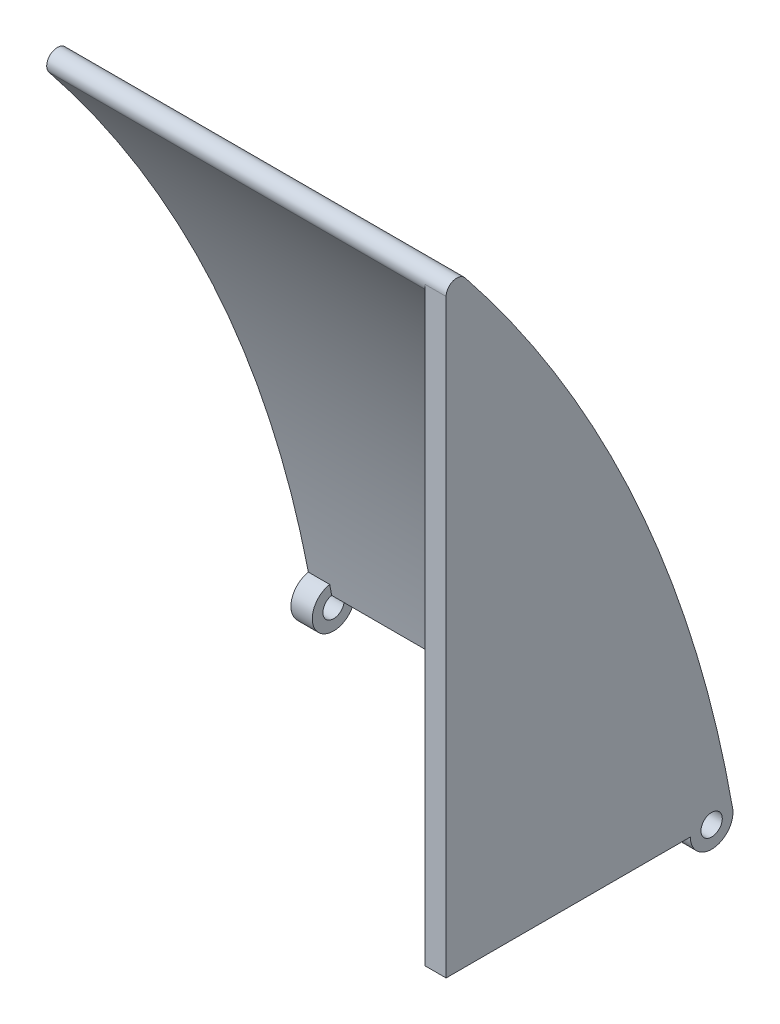
SolidWorks part; units mm, degrees
ref_plane "Front Plane" through (0, 0, 0) normal (0, 0, 1) x (1, 0, 0)
ref_plane "Top Plane" through (0, 0, 0) normal (0, 1, 0) x (1, 0, 0)
ref_plane "Right Plane" through (0, 0, 0) normal (1, 0, 0) x (0, 0, -1)
sketch "Sketch9" plane through (0, 0, 0) normal (1, 0, 0) x (0, 0, -1)
  line L0 (0, 0) -> (-50000, 0) construction
  line L1 (0, 0) -> (0, 50000) construction
  line L2 (0, 0) -> (-0.1736, 0.9848)
  line L3 (-5.0771, 0) -> (-5.0977, 0.1166)
  line L4 (0, 0) -> (-5.0771, 0)
  line L7 (-4.924, -0.8682) -> (-5.0977, 0.1166) construction
  arc A0 (-0.1736, 0.9848) -> (-62.9066, 140) centre (-304.4663, -52.6702) ccw
  arc A1 (-5.0977, 0.1166) -> (-66.8155, 136.8822) centre (-304.4663, -52.6702) ccw
  arc A2 (-66.8155, 136.8822) -> (-62.9066, 140) centre (-64.8611, 138.4411) cw
  dimension "D1" = 10
  dimension "D2" = 1
  dimension "D3" = 140
  dimension "D5" = 66.8155
  dimension "D4" = 5
extrude "Boss-Extrude8" add sketch "Sketch9" along normal mid plane 93.68
sketch "Sketch10" plane through (46.84, 0, 0) normal (1, 0, 0) x (0, 0, -1)
  circle A0 centre (-5.0771, 0) radius 5
  dimension "D1" = 10
extrude "Boss-Extrude9" add sketch "Sketch10" against normal blind 5
mirror "Mirror1" about plane through (0, 0, 0) normal (1, 0, 0) of "Boss-Extrude9"
sketch "Sketch11" plane through (46.84, 0, 0) normal (1, 0, 0) x (0, 0, -1)
  circle A1 centre (-5.0771, 0) radius 2.5
  dimension "D1" = 5
extrude "Cut-Extrude4" cut sketch "Sketch11" against normal through all
sketch "Sketch13" plane through (46.84, 0, 0) normal (1, 0, 0) x (0, 0, -1)
  line L0 (-10.0771, 0) -> (-67.3611, 0)
  line L1 (-67.3611, 0) -> (-67.3611, 138.4411)
  line L2 (-64.8611, 138.4411) -> (-67.3611, 138.4411) construction
  line L3 (-5.0771, 0) -> (49994.9229, 0) construction
  arc A0 (-5.9839, 4.9171) -> (-0.0771, 0) centre (-5.0771, 0) ccw construction
  arc A1 (-5.9839, 4.9171) -> (-10.0771, 0) centre (-5.0771, 0) ccw
  arc A2 (-67.3611, 138.4411) -> (-66.8155, 136.8822) centre (-64.8611, 138.4411) ccw
  arc A3 (-5.9839, 4.9171) -> (-66.8155, 136.8822) centre (-304.4663, -52.6702) ccw
  arc A4 (-5.9839, 4.9171) -> (-66.8155, 136.8822) centre (-304.4663, -52.6702) ccw construction
  arc A7 (-62.9066, 140) -> (-66.8155, 136.8822) centre (-64.8611, 138.4411) ccw construction
  point P28 (-28.3986, 74.5879)
  dimension "D1" = 90
extrude "Boss-Extrude10" add sketch "Sketch13" against normal blind 5
